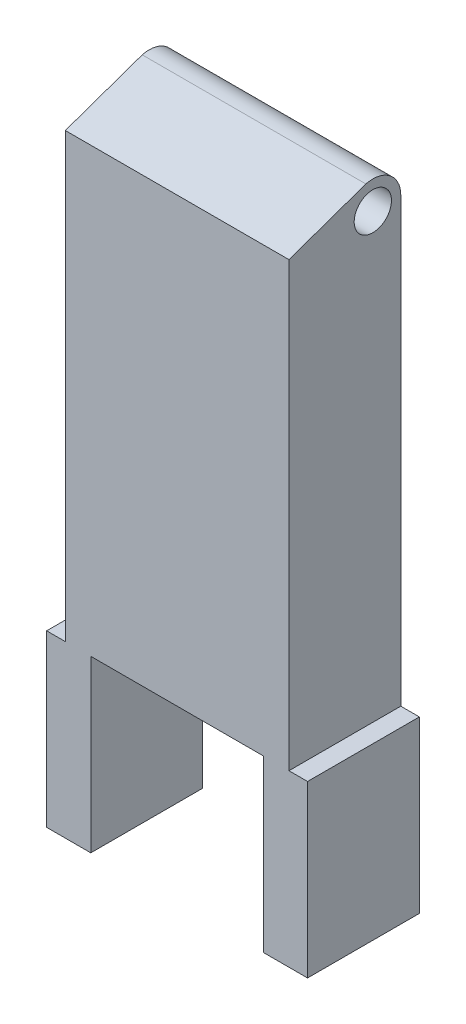
SolidWorks part; units mm, degrees
ref_plane "정면" through (0, 0, 0) normal (0, 0, 1) x (1, 0, 0)
ref_plane "윗면" through (0, 0, 0) normal (0, 1, 0) x (1, 0, 0)
ref_plane "우측면" through (0, 0, 0) normal (1, 0, 0) x (0, 0, -1)
sketch "스케치1" plane through (0, 0, 0) normal (0, 0, 1) x (1, 0, 0)
  line L0 (-11.9944, 44.775) -> (-11.9944, -2.725)
  line L1 (-11.9944, 44.775) -> (12.0056, 44.775)
  line L2 (12.0056, 44.775) -> (12.0056, -2.7271)
  line L3 (9.2615, -20.9932) -> (14.0002, -20.9932)
  line L4 (14.0002, -2.7271) -> (12.0056, -2.7271)
  line L5 (-11.9944, -2.725) -> (-13.9998, -2.725)
  line L9 (0.0056, 44.775) -> (0.0056, -20.9932) construction
  line L10 (9.2615, -2.7271) -> (-9.2611, -2.725)
  line L12 (9.2615, -20.9932) -> (9.2615, -2.7271)
  line L14 (14.0002, -20.9932) -> (14.0002, -2.7271)
  line L15 (-9.2611, -20.9932) -> (-13.9998, -20.9932)
  line L16 (-9.2611, -20.9932) -> (-9.2611, -2.725)
  line L18 (-13.9998, -20.9932) -> (-13.9998, -2.725)
  dimension "D2" = 12
  dimension "D1" = 47.5
extrude "보스-돌출1" add sketch "스케치1" along normal blind 12
ref_plane "평면11" through (12.0056, 0, 0) normal (1, 0, 0) x (0, 0, -1)
ref_plane "평면12" through (12.0056, 0, 0) normal (1, 0, 0) x (0, 0, -1)
sketch "스케치15" plane through (12.0056, 0, 0) normal (1, 0, 0) x (0, 0, -1)
  line L0 (-12, 44.775) -> (0, 44.775) construction
  line L1 (0, -2.7271) -> (0, 44.775) construction
  line L2 (-12, 44.775) -> (-3.7467, 47.6806)
  line L3 (0, 44.775) -> (-12, 44.775)
  arc A0 (0, 44.775) -> (-3.7467, 47.6806) centre (-3, 44.775) ccw
  dimension "D1" = 6
extrude "보스-돌출4" add sketch "스케치15" against normal blind 24
sketch "스케치16" plane through (12.0056, 0, 0) normal (1, 0, 0) x (0, 0, -1)
  circle A0 centre (-3, 44.775) radius 2
  dimension "D1" = 4
extrude "컷-돌출11" cut sketch "스케치16" against normal through all
ref_plane "평면13" through (0.0056, 0, 0) normal (1, 0, 0) x (0, 0, -1)
sketch "스케치17" plane through (0, 0, 0) normal (0, 0, -1) x (-1, 0, 0)
  line L0 (-12.0056, 44.775) -> (11.9944, 44.775) construction
  point P0 (-0.0056, 44.775)
ref_plane "평면14" through (14.0002, 0, 0) normal (1, 0, 0) x (0, 0, -1)
sketch "스케치20" plane through (14.0002, 0, 0) normal (1, 0, 0) x (0, 0, -1)
  line L0 (-4.3834, -12.1932) -> (-7.6166, -12.1932)
  line L1 (-7.6166, -12.1932) -> (-9.2332, -14.9932)
  line L2 (-9.2332, -14.9932) -> (-7.6166, -17.7932)
  line L3 (-7.6166, -17.7932) -> (-4.3834, -17.7932)
  line L4 (-4.3834, -17.7932) -> (-2.7668, -14.9932)
  line L5 (-2.7668, -14.9932) -> (-4.3834, -12.1932)
  line L6 (-7.6166, -12.1932) -> (-4.3834, -17.7932) construction
  line L7 (-4.3834, -12.1932) -> (-7.6166, -17.7932) construction
  line L8 (-9.2332, -14.9932) -> (-2.7668, -14.9932) construction
  line L9 (-12, -20.9932) -> (0, -20.9932) construction
  line L10 (0, -20.9932) -> (0, -2.7271) construction
  point P2 (-6, -14.9932)
  dimension "D1" = 3.2332
  dimension "D2" = 3.2332
  dimension "D3" = 3.2332
  dimension "D4" = 3.2332
  dimension "D5" = 3.2332
  dimension "D6" = 3.2332
  dimension "D7" = 6
  dimension "D8" = 6
